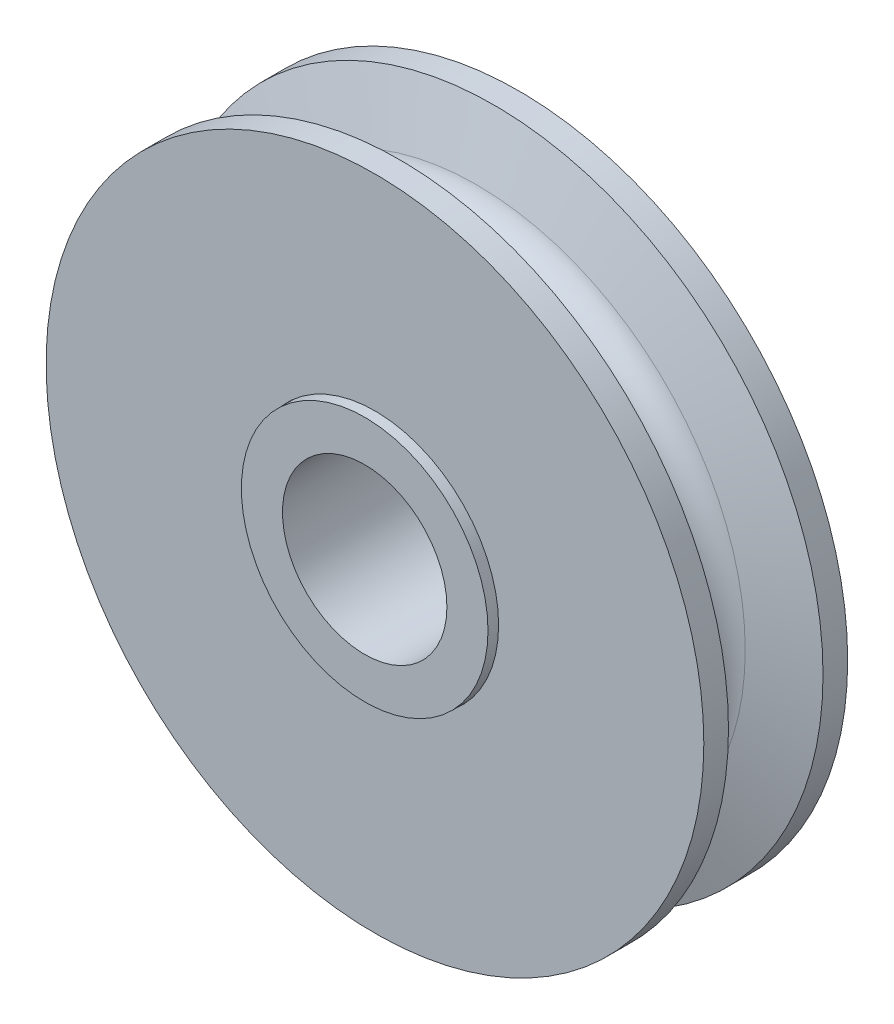
SolidWorks part; units mm, degrees
ref_plane "Front" through (0, 0, 0) normal (0, 0, 1) x (1, 0, 0)
ref_plane "Top" through (0, 0, 0) normal (0, 1, 0) x (1, 0, 0)
ref_plane "Right" through (0, 0, 0) normal (1, 0, 0) x (0, 0, -1)
sketch "Sketch1" plane through (0, 0, 0) normal (1, 0, 0) x (0, 0, -1)
  line L0 (3.6513, 25.4) -> (5.5562, 25.4)
  line L1 (-3.6512, 25.4) -> (-5.5562, 25.4)
  line L2 (-3.6512, 25.4) -> (-2.2842, 20.7585)
  line L4 (6.35, 6.35) -> (-6.35, 6.35)
  line L6 (3.6513, 25.4) -> (2.2842, 20.7585)
  line L8 (-6.35, 0) -> (6.35, 0) construction
  line L9 (-5.5562, 9.525) -> (-5.5562, 25.4)
  line L10 (5.5562, 25.4) -> (5.5563, 9.525)
  line L12 (-5.5562, 9.525) -> (-6.35, 9.525)
  line L13 (-6.35, 9.525) -> (-6.35, 6.35)
  line L14 (0, 19.05) -> (0, -19.05) construction
  line L15 (6.35, 9.525) -> (5.5563, 9.525)
  line L16 (6.35, 9.525) -> (6.35, 6.35)
  line L17 (-5.5562, 25.4) -> (-5.5562, -25.4) construction
  arc A0 (-2.2842, 20.7585) -> (2.2842, 20.7585) centre (0, 21.4312) ccw
  circle A1 centre (0, 21.4312) radius 2.3813 construction
  circle A2 centre (0, 0) radius 6.35 construction
  circle A3 centre (0, 0) radius 9.525 construction
  circle A4 centre (0, 0) radius 15.875 construction
  circle A5 centre (0, -21.4313) radius 2.3812 construction
  point P28 (-5.5562, 0)
  dimension "Rope Dia" = 4.7625
  dimension "Shaft Dia" = 12.7
  dimension "D1" = 19.05
  dimension "D3" = 31.75
  dimension "Wd" = 12.7
  dimension "D8" = 1.905
  dimension "Groove Dia" = 38.1
  dimension "OD" = 50.8
  dimension "w Wd" = 11.1125
revolve "Revolve1" add sketch "Sketch1" angle 360 about L8
sketch "Sketch2" plane through (0, 0, 0) normal (0, 0, 1) x (1, 0, 0)
  circle A0 centre (0, 0) radius 9.525 construction
  circle A1 centre (0, 0) radius 9.525
extrude "Cut-Extrude-Thin1" cut sketch "Sketch2" against normal through all and the other way through all thin
equation "\"D8@Sketch1\" = \"Wd@Sketch1\" * .15"
equation "\"D1@Sketch1\" = \"Shaft Dia@Sketch1\" * 1.5"
equation "\"D3@Sketch1\" = \"Shaft Dia@Sketch1\" * 2.5"
